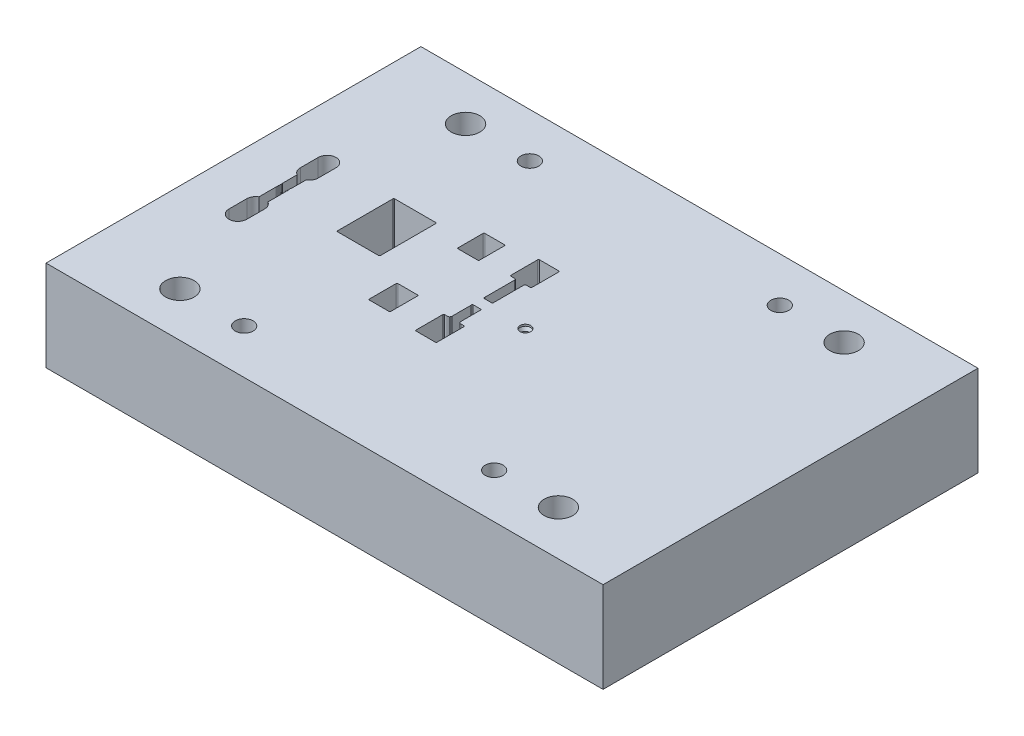
SolidWorks part; units mm, degrees
ref_plane "Front" through (0, 0, 0) normal (0, 0, 1) x (1, 0, 0)
ref_plane "Top" through (0, 0, 0) normal (0, 1, 0) x (1, 0, 0)
ref_plane "Right" through (0, 0, 0) normal (1, 0, 0) x (0, 0, -1)
sketch "Sketch1" plane through (0, 0, 0) normal (0, 0, 1) x (1, 0, 0)
  line L1 (-78, 0) -> (78, 0)
  line L2 (-78, 0) -> (-78, 25.4)
  line L3 (-78, 25.4) -> (78, 25.4)
  line L4 (78, 0) -> (78, 25.4)
  dimension "D1" = 78
  dimension "D2" = 25.4
  dimension "D3" = 78
extrude "Extrude1" add sketch "Sketch1" along normal mid plane 105
hole_wizard "M6 Tapped Hole1" positions "Sketch3" profile "Sketch2" tap size "M6" standard "ISO"
sketch "Sketch3" plane through (0, 25.4, 0) normal (0, 1, 0) x (-1, 0, 0)
  point P1 (35, -40)
  point P4 (-35, -40)
  point P13 (-35, 40)
  point P16 (35, 40)
sketch "Sketch2" plane through (-35, 25.4, -40) normal (1, 0, 0) x (0, 0, 1)
  line L0 (0, 0) -> (0, 16.5022)
  line L1 (0, 16.5022) -> (2.5, 15)
  line L2 (2.5, 15) -> (2.5, 0)
  line L5 (2.5, 0) -> (0, 0)
  line L10 (0, 16.5022) -> (-2.5, 15) construction
  line L11 (0, -6.35) -> (0, 107.95) construction
  dimension "Tap Drill Dia." = 5
  dimension "Tap Drill Depth" = 15
  dimension "Drill Angle" = 118
cosmetic thread "Hole Thread1" parameters "D1"=10, "D2"=6
cosmetic thread "Hole Thread2" parameters "D1"=10, "D2"=6
cosmetic thread "Hole Thread5" parameters "D1"=10, "D2"=6
cosmetic thread "Hole Thread6" parameters "D1"=10, "D2"=6
hole_wizard "Hole1" positions "Sketch5" profile "Sketch4" legacy end condition through all
sketch "Sketch5" plane through (0, 25.4, 0) normal (0, 1, 0) x (-1, 0, 0)
  point P1 (53, -40)
  point P6 (53, 40)
  point P9 (-53, 40)
  point P12 (-53, -40)
sketch "Sketch4" plane through (-53, 25.4, -40) normal (1, 0, 0) x (0, 0, 1)
  line L0 (0, 0) -> (0, 25.4)
  line L1 (0, 25.4) -> (4, 25.4)
  line L2 (4, 25.4) -> (4, 0)
  line L3 (4, 0) -> (0, 0)
  line L4 (0, 110) -> (0, -10) construction
  dimension "Diameter" = 8
  dimension "Depth" = 25.4
sketch "Sketch6" plane through (0, 25.4, 0) normal (0, 1, 0) x (1, 0, 0)
  line L0 (-61.75, -6.7884) -> (-61.5151, -7.4339)
  line L2 (-64.25, -6.7884) -> (-64.4849, -7.4339)
  line L4 (-18.25, -8.1954) -> (-23.75, -8.1954)
  line L5 (-24, -8.4454) -> (-24, -15.9454)
  line L6 (-23.75, -16.1954) -> (-18.25, -16.1954)
  line L7 (-18, -15.9454) -> (-18, -8.4454)
  line L8 (-18.25, -8.1954) -> (-23.75, -8.1954)
  line L9 (-24, -8.4454) -> (-24, -15.9454)
  line L10 (-23.75, -16.1954) -> (-18.25, -16.1954)
  line L11 (-18, -15.9454) -> (-18, -8.4454)
  line L12 (-18.25, 16.15) -> (-23.75, 16.15)
  line L13 (-24, 15.9) -> (-24, 8.9)
  line L14 (-23.75, 8.65) -> (-18.25, 8.65)
  line L15 (-18, 8.9) -> (-18, 15.9)
  line L16 (-18.25, 16.15) -> (-23.75, 16.15)
  line L17 (-24, 15.9) -> (-24, 8.9)
  line L18 (-23.75, 8.65) -> (-18.25, 8.65)
  line L19 (-18, 8.9) -> (-18, 15.9)
  line L20 (-33, -3.8454) -> (-33, 11.6546)
  line L21 (-39, -4.0954) -> (-33.25, -4.0954)
  line L22 (-39, 11.9046) -> (-39, -4.0954)
  line L23 (-33.25, 11.9046) -> (-39, 11.9046)
  line L24 (-33, -3.8454) -> (-33, 11.6546)
  line L28 (-44.75, -4.0954) -> (-39, -4.0954)
  line L29 (-39, -4.0954) -> (-39, 11.9046)
  line L30 (-39, 11.9046) -> (-44.75, 11.9046)
  line L31 (-45, 11.6546) -> (-45, -3.8454)
  line L32 (-44.75, -4.0954) -> (-33.25, -4.0954)
  line L34 (-33.25, 11.9046) -> (-44.75, 11.9046)
  line L35 (-45, 11.6546) -> (-45, -3.8454)
  line L38 (-61.75, -3.1454) -> (-61.75, -1.7954)
  line L39 (-61.75, 0.0046) -> (-61.75, 0.6066)
  line L40 (-62, 0.8566) -> (-64, 0.8566)
  line L41 (-64.25, 0.6066) -> (-64.25, 0.0046)
  line L42 (-64.25, -1.7954) -> (-64.25, -3.1454)
  line L43 (-64, -3.3954) -> (-62, -3.3954)
  line L44 (-9, -9.1754) -> (-9.7, -9.1754)
  line L45 (-9.95, -9.4254) -> (-9.95, -16.9254)
  line L46 (-9.7, -17.1754) -> (-4.3, -17.1754)
  line L47 (-4.05, -16.9254) -> (-4.05, -9.4254)
  line L48 (-4.3, -9.1754) -> (-5, -9.1754)
  line L49 (-5.6073, -8.9669) -> (-5.7285, -8.582)
  line L50 (-5.74, -8.5069) -> (-5.74, -3.2709)
  line L51 (-5.7249, -3.1854) -> (-5.7051, -3.1309)
  line L52 (-5.94, -2.7954) -> (-8.06, -2.7954)
  line L53 (-8.2949, -3.1309) -> (-8.2751, -3.1854)
  line L54 (-8.26, -3.2709) -> (-8.26, -8.5069)
  line L55 (-8.2715, -8.582) -> (-8.3927, -8.9669)
  line L56 (-9, -9.1754) -> (-9.7, -9.1754)
  line L57 (-9.95, -9.4254) -> (-9.95, -16.9254)
  line L58 (-9.7, -17.1754) -> (-4.3, -17.1754)
  line L59 (-4.05, -16.9254) -> (-4.05, -9.4254)
  line L60 (-4.3, -9.1754) -> (-5, -9.1754)
  line L61 (-5.6073, -8.9669) -> (-5.7285, -8.582)
  line L62 (-5.74, -8.5069) -> (-5.74, -3.2709)
  line L63 (-5.7249, -3.1854) -> (-5.7051, -3.1309)
  line L64 (-5.94, -2.7954) -> (-8.06, -2.7954)
  line L65 (-8.2949, -3.1309) -> (-8.2751, -3.1854)
  line L66 (-8.26, -3.2709) -> (-8.26, -8.5069)
  line L67 (-8.2715, -8.582) -> (-8.3927, -8.9669)
  line L68 (-5.4106, 9.4) -> (-4.3, 9.4)
  line L69 (-5.7003, 9.1618) -> (-5.6209, 9.2852)
  line L70 (-5.74, 0.7046) -> (-5.74, 9.0266)
  line L71 (-5.7151, 0.5921) -> (-5.7249, 0.6191)
  line L72 (-8.05, 0.2566) -> (-5.95, 0.2566)
  line L73 (-8.2751, 0.6191) -> (-8.2849, 0.5921)
  line L74 (-8.26, 9.0266) -> (-8.26, 0.7046)
  line L75 (-8.3791, 9.2852) -> (-8.2997, 9.1618)
  line L76 (-9.7, 9.4) -> (-8.5894, 9.4)
  line L77 (-9.95, 17.15) -> (-9.95, 9.65)
  line L78 (-4.3, 17.4) -> (-9.7, 17.4)
  line L79 (-4.05, 9.65) -> (-4.05, 17.15)
  line L80 (-5.4106, 9.4) -> (-4.3, 9.4)
  line L81 (-5.7003, 9.1618) -> (-5.6209, 9.2852)
  line L82 (-5.74, 0.7046) -> (-5.74, 9.0266)
  line L83 (-5.7151, 0.5921) -> (-5.7249, 0.6191)
  line L84 (-8.05, 0.2566) -> (-5.95, 0.2566)
  line L85 (-8.2751, 0.6191) -> (-8.2849, 0.5921)
  line L86 (-8.26, 9.0266) -> (-8.26, 0.7046)
  line L87 (-8.3791, 9.2852) -> (-8.2997, 9.1618)
  line L88 (-9.7, 9.4) -> (-8.5894, 9.4)
  line L89 (-9.95, 17.15) -> (-9.95, 9.65)
  line L90 (-4.3, 17.4) -> (-9.7, 17.4)
  line L91 (-4.05, 9.65) -> (-4.05, 17.15)
  line L92 (-61.75, -6.7884) -> (-61.75, -1.7954)
  line L93 (-61.75, 0.0046) -> (-61.75, 4.2497)
  line L95 (-64.25, 4.2497) -> (-64.25, 0.0046)
  line L96 (-64.25, -1.7954) -> (-64.25, -6.7884)
  line L162 (-61.75, -7.7694) -> (-64.25, -7.7694) construction
  line L163 (-64.25, 5.2306) -> (-61.75, 5.2306) construction
  line L164 (-61.75, -7.7694) -> (-64.25, -7.7694)
  line L165 (-64.25, 5.2306) -> (-61.75, 5.2306)
  line L166 (-64.25, 7.2306) -> (-64.25, 0.0046) construction
  line L167 (-64.25, 4.2497) -> (-64.4849, 4.8951)
  line L168 (-63, 5.2306) -> (-63, 5.7564) construction
  line L169 (-61.75, 4.2497) -> (-61.5151, 4.8951)
  line L170 (-63, 5.2306) -> (-63, -7.7694) construction
  line L171 (-63, -1.2694) -> (-59.6995, -1.2694) construction
  arc A0 (-61.5151, -7.4339) -> (-61.75, -7.7694) centre (-61.75, -7.5194) cw
  arc A1 (-64.4849, -7.4339) -> (-64.25, -7.7694) centre (-64.25, -7.5194) ccw
  arc A2 (-33.25, -4.0954) -> (-33, -3.8454) centre (-33.25, -3.8454) ccw
  arc A3 (-33, 11.6546) -> (-33.25, 11.9046) centre (-33.25, 11.6546) ccw
  arc A4 (-23.75, -8.1954) -> (-24, -8.4454) centre (-23.75, -8.4454) ccw
  arc A5 (-24, -15.9454) -> (-23.75, -16.1954) centre (-23.75, -15.9454) ccw
  arc A6 (-18.25, -16.1954) -> (-18, -15.9454) centre (-18.25, -15.9454) ccw
  arc A7 (-18, -8.4454) -> (-18.25, -8.1954) centre (-18.25, -8.4454) ccw
  arc A8 (-23.75, -8.1954) -> (-24, -8.4454) centre (-23.75, -8.4454) ccw
  arc A9 (-24, -15.9454) -> (-23.75, -16.1954) centre (-23.75, -15.9454) ccw
  arc A10 (-18.25, -16.1954) -> (-18, -15.9454) centre (-18.25, -15.9454) ccw
  arc A11 (-18, -8.4454) -> (-18.25, -8.1954) centre (-18.25, -8.4454) ccw
  arc A12 (-23.75, 16.15) -> (-24, 15.9) centre (-23.75, 15.9) ccw
  arc A13 (-24, 8.9) -> (-23.75, 8.65) centre (-23.75, 8.9) ccw
  arc A14 (-18.25, 8.65) -> (-18, 8.9) centre (-18.25, 8.9) ccw
  arc A15 (-18, 15.9) -> (-18.25, 16.15) centre (-18.25, 15.9) ccw
  arc A16 (-23.75, 16.15) -> (-24, 15.9) centre (-23.75, 15.9) ccw
  arc A17 (-24, 8.9) -> (-23.75, 8.65) centre (-23.75, 8.9) ccw
  arc A18 (-18.25, 8.65) -> (-18, 8.9) centre (-18.25, 8.9) ccw
  arc A19 (-18, 15.9) -> (-18.25, 16.15) centre (-18.25, 15.9) ccw
  arc A20 (-33.25, -4.0954) -> (-33, -3.8454) centre (-33.25, -3.8454) ccw
  arc A21 (-33, 11.6546) -> (-33.25, 11.9046) centre (-33.25, 11.6546) ccw
  arc A22 (-44.75, 11.9046) -> (-45, 11.6546) centre (-44.75, 11.6546) ccw
  arc A23 (-45, -3.8454) -> (-44.75, -4.0954) centre (-44.75, -3.8454) ccw
  arc A24 (-44.75, 11.9046) -> (-45, 11.6546) centre (-44.75, 11.6546) ccw
  arc A25 (-45, -3.8454) -> (-44.75, -4.0954) centre (-44.75, -3.8454) ccw
  arc A38 (-5.4106, 9.4) -> (-5.6209, 9.2852) centre (-5.4106, 9.15) ccw
  arc A39 (-5.7003, 9.1618) -> (-5.74, 9.0266) centre (-5.49, 9.0266) ccw
  arc A40 (-5.74, 0.7046) -> (-5.7249, 0.6191) centre (-5.49, 0.7046) ccw
  arc A41 (-5.95, 0.2566) -> (-5.7151, 0.5921) centre (-5.95, 0.5066) ccw
  arc A42 (-9.7, -9.1754) -> (-9.95, -9.4254) centre (-9.7, -9.4254) ccw
  arc A43 (-9.95, -16.9254) -> (-9.7, -17.1754) centre (-9.7, -16.9254) ccw
  arc A44 (-4.3, -17.1754) -> (-4.05, -16.9254) centre (-4.3, -16.9254) ccw
  arc A45 (-4.05, -9.4254) -> (-4.3, -9.1754) centre (-4.3, -9.4254) ccw
  arc A46 (-5.4806, -9.0963) -> (-5, -9.1754) centre (-5, -7.6754) ccw
  arc A47 (-5.5312, -9.0707) -> (-5.4806, -9.0963) centre (-5.4165, -8.9068) ccw
  arc A48 (-5.6073, -8.9669) -> (-5.5312, -9.0707) centre (-5.4165, -8.9068) ccw
  arc A49 (-5.74, -8.5069) -> (-5.7285, -8.582) centre (-5.49, -8.5069) ccw
  arc A50 (-5.7249, -3.1854) -> (-5.74, -3.2709) centre (-5.49, -3.2709) ccw
  arc A51 (-5.7051, -3.1309) -> (-5.94, -2.7954) centre (-5.94, -3.0454) ccw
  arc A52 (-8.06, -2.7954) -> (-8.2949, -3.1309) centre (-8.06, -3.0454) ccw
  arc A53 (-8.26, -3.2709) -> (-8.2751, -3.1854) centre (-8.51, -3.2709) ccw
  arc A54 (-8.2715, -8.582) -> (-8.26, -8.5069) centre (-8.51, -8.5069) ccw
  arc A55 (-8.4688, -9.0707) -> (-8.3927, -8.9669) centre (-8.5835, -8.9068) ccw
  arc A56 (-8.5194, -9.0963) -> (-8.4688, -9.0707) centre (-8.5835, -8.9068) ccw
  arc A57 (-9, -9.1754) -> (-8.5194, -9.0963) centre (-9, -7.6754) ccw
  arc A58 (-9.7, -9.1754) -> (-9.95, -9.4254) centre (-9.7, -9.4254) ccw
  arc A59 (-9.95, -16.9254) -> (-9.7, -17.1754) centre (-9.7, -16.9254) ccw
  arc A60 (-4.3, -17.1754) -> (-4.05, -16.9254) centre (-4.3, -16.9254) ccw
  arc A61 (-4.05, -9.4254) -> (-4.3, -9.1754) centre (-4.3, -9.4254) ccw
  arc A62 (-5.4806, -9.0963) -> (-5, -9.1754) centre (-5, -7.6754) ccw
  arc A63 (-5.5312, -9.0707) -> (-5.4806, -9.0963) centre (-5.4165, -8.9068) ccw
  arc A64 (-5.6073, -8.9669) -> (-5.5312, -9.0707) centre (-5.4165, -8.9068) ccw
  arc A65 (-5.74, -8.5069) -> (-5.7285, -8.582) centre (-5.49, -8.5069) ccw
  arc A66 (-5.7249, -3.1854) -> (-5.74, -3.2709) centre (-5.49, -3.2709) ccw
  arc A67 (-5.7051, -3.1309) -> (-5.94, -2.7954) centre (-5.94, -3.0454) ccw
  arc A68 (-8.06, -2.7954) -> (-8.2949, -3.1309) centre (-8.06, -3.0454) ccw
  arc A69 (-8.26, -3.2709) -> (-8.2751, -3.1854) centre (-8.51, -3.2709) ccw
  arc A70 (-8.2715, -8.582) -> (-8.26, -8.5069) centre (-8.51, -8.5069) ccw
  arc A71 (-8.4688, -9.0707) -> (-8.3927, -8.9669) centre (-8.5835, -8.9068) ccw
  arc A72 (-8.5194, -9.0963) -> (-8.4688, -9.0707) centre (-8.5835, -8.9068) ccw
  arc A73 (-9, -9.1754) -> (-8.5194, -9.0963) centre (-9, -7.6754) ccw
  arc A74 (-8.2849, 0.5921) -> (-8.05, 0.2566) centre (-8.05, 0.5066) ccw
  arc A75 (-8.2751, 0.6191) -> (-8.26, 0.7046) centre (-8.51, 0.7046) ccw
  arc A76 (-8.26, 9.0266) -> (-8.2997, 9.1618) centre (-8.51, 9.0266) ccw
  arc A77 (-8.3791, 9.2852) -> (-8.5894, 9.4) centre (-8.5894, 9.15) ccw
  arc A78 (-9.95, 9.65) -> (-9.7, 9.4) centre (-9.7, 9.65) ccw
  arc A79 (-9.7, 17.4) -> (-9.95, 17.15) centre (-9.7, 17.15) ccw
  arc A80 (-4.05, 17.15) -> (-4.3, 17.4) centre (-4.3, 17.15) ccw
  arc A81 (-4.3, 9.4) -> (-4.05, 9.65) centre (-4.3, 9.65) ccw
  arc A82 (-5.4106, 9.4) -> (-5.6209, 9.2852) centre (-5.4106, 9.15) ccw
  arc A83 (-5.7003, 9.1618) -> (-5.74, 9.0266) centre (-5.49, 9.0266) ccw
  arc A84 (-5.74, 0.7046) -> (-5.7249, 0.6191) centre (-5.49, 0.7046) ccw
  arc A85 (-5.95, 0.2566) -> (-5.7151, 0.5921) centre (-5.95, 0.5066) ccw
  arc A86 (-8.2849, 0.5921) -> (-8.05, 0.2566) centre (-8.05, 0.5066) ccw
  arc A87 (-8.2751, 0.6191) -> (-8.26, 0.7046) centre (-8.51, 0.7046) ccw
  arc A88 (-8.26, 9.0266) -> (-8.2997, 9.1618) centre (-8.51, 9.0266) ccw
  arc A89 (-8.3791, 9.2852) -> (-8.5894, 9.4) centre (-8.5894, 9.15) ccw
  arc A90 (-9.95, 9.65) -> (-9.7, 9.4) centre (-9.7, 9.65) ccw
  arc A91 (-9.7, 17.4) -> (-9.95, 17.15) centre (-9.7, 17.15) ccw
  arc A92 (-4.05, 17.15) -> (-4.3, 17.4) centre (-4.3, 17.15) ccw
  arc A93 (-4.3, 9.4) -> (-4.05, 9.65) centre (-4.3, 9.65) ccw
  arc A100 (-61.75, -1.7954) -> (-61.8, -1.6454) centre (-62, -1.7954) ccw
  arc A101 (-61.8, -1.3454) -> (-61.8, -1.6454) centre (-61.6, -1.4954) ccw
  arc A102 (-61.8, -1.3454) -> (-61.8, -1.0454) centre (-62, -1.1954) ccw
  arc A103 (-61.8, -0.7454) -> (-61.8, -1.0454) centre (-61.6, -0.8954) ccw
  arc A104 (-61.8, -0.7454) -> (-61.8, -0.4454) centre (-62, -0.5954) ccw
  arc A105 (-61.8, -0.1454) -> (-61.8, -0.4454) centre (-61.6, -0.2954) ccw
  arc A106 (-61.8, -0.1454) -> (-61.75, 0.0046) centre (-62, 0.0046) ccw
  arc A107 (-61.75, 0.6066) -> (-62, 0.8566) centre (-62, 0.6066) ccw
  arc A108 (-64, 0.8566) -> (-64.25, 0.6066) centre (-64, 0.6066) ccw
  arc A109 (-64.25, 0.0046) -> (-64.2, -0.1454) centre (-64, 0.0046) ccw
  arc A110 (-64.2, -0.4454) -> (-64.2, -0.1454) centre (-64.4, -0.2954) ccw
  arc A111 (-64.2, -0.4454) -> (-64.2, -0.7454) centre (-64, -0.5954) ccw
  arc A112 (-64.2, -1.0454) -> (-64.2, -0.7454) centre (-64.4, -0.8954) ccw
  arc A113 (-64.2, -1.0454) -> (-64.2, -1.3454) centre (-64, -1.1954) ccw
  arc A114 (-64.2, -1.6454) -> (-64.2, -1.3454) centre (-64.4, -1.4954) ccw
  arc A115 (-64.2, -1.6454) -> (-64.25, -1.7954) centre (-64, -1.7954) ccw
  arc A116 (-64.25, -3.1454) -> (-64, -3.3954) centre (-64, -3.1454) ccw
  arc A117 (-62, -3.3954) -> (-61.75, -3.1454) centre (-62, -3.1454) ccw
  arc A118 (-61.75, -1.7954) -> (-61.8, -1.6454) centre (-62, -1.7954) ccw
  arc A119 (-61.8, -1.3454) -> (-61.8, -1.6454) centre (-61.6, -1.4954) ccw
  arc A120 (-61.8, -1.3454) -> (-61.8, -1.0454) centre (-62, -1.1954) ccw
  arc A121 (-61.8, -0.7454) -> (-61.8, -1.0454) centre (-61.6, -0.8954) ccw
  arc A122 (-61.8, -0.7454) -> (-61.8, -0.4454) centre (-62, -0.5954) ccw
  arc A123 (-61.8, -0.1454) -> (-61.8, -0.4454) centre (-61.6, -0.2954) ccw
  arc A124 (-61.8, -0.1454) -> (-61.75, 0.0046) centre (-62, 0.0046) ccw
  arc A127 (-64.25, 0.0046) -> (-64.2, -0.1454) centre (-64, 0.0046) ccw
  arc A128 (-64.2, -0.4454) -> (-64.2, -0.1454) centre (-64.4, -0.2954) ccw
  arc A129 (-64.2, -0.4454) -> (-64.2, -0.7454) centre (-64, -0.5954) ccw
  arc A130 (-64.2, -1.0454) -> (-64.2, -0.7454) centre (-64.4, -0.8954) ccw
  arc A131 (-64.2, -1.0454) -> (-64.2, -1.3454) centre (-64, -1.1954) ccw
  arc A132 (-64.2, -1.6454) -> (-64.2, -1.3454) centre (-64.4, -1.4954) ccw
  arc A133 (-64.2, -1.6454) -> (-64.25, -1.7954) centre (-64, -1.7954) ccw
  arc A210 (-64.4849, 4.8951) -> (-64.25, 5.2306) centre (-64.25, 4.9806) cw
  arc A211 (-61.5151, 4.8951) -> (-61.75, 5.2306) centre (-61.75, 4.9806) ccw
  dimension "D5" = 0.25
  dimension "D9" = 20
  dimension "D1" = 0
  dimension "D2" = 0
  dimension "D3" = 0
  dimension "D4" = 0
  dimension "D6" = 0
  dimension "D7" = 0
  dimension "D8" = 0
extrude "Cut-Extrude1" cut sketch "Sketch6" against normal through all
sketch "Sketch7" plane through (0, 25.4, 0) normal (0, 1, 0) x (1, 0, 0)
  line L0 (-63, -7.7694) -> (-63, 6.2306) construction
  line L1 (-64.25, -7.7694) -> (-61.75, -7.7694) construction
  line L2 (-63, 5.2306) -> (-63, -8.7694) construction
  line L4 (-63, 6.2306) -> (-63, 11.2306) construction
  line L5 (-65.5, 6.2306) -> (-65.5, 11.2306)
  line L6 (-60.5, 6.2306) -> (-60.5, 11.2306)
  line L7 (-63, -8.7694) -> (-63, -13.7694) construction
  line L8 (-60.5, -8.7694) -> (-60.5, -13.7694)
  line L9 (-65.5, -8.7694) -> (-65.5, -13.7694)
  line L10 (-62.5414, 5.2306) -> (-62.5414, -7.7694) construction
  line L11 (-61.75, 5.2306) -> (-64.25, 5.2306) construction
  line L12 (-64.25, -7.7694) -> (-61.75, -7.7694) construction
  line L13 (-62.5414, -1.2694) -> (-59.6733, -1.2694) construction
  line L14 (-63, 8.7306) -> (-59.6733, 8.7306) construction
  line L15 (-63, -11.2694) -> (-59.6733, -11.2694) construction
  line L16 (-59.6733, -11.2694) -> (-59.6733, 8.7306) construction
  arc A0 (-65.5, 6.2306) -> (-60.5, 6.2306) centre (-63, 6.2306) ccw
  arc A1 (-60.5, 11.2306) -> (-65.5, 11.2306) centre (-63, 11.2306) ccw
  arc A2 (-60.5, -8.7694) -> (-65.5, -8.7694) centre (-63, -8.7694) ccw
  arc A3 (-65.5, -13.7694) -> (-60.5, -13.7694) centre (-63, -13.7694) ccw
  point P1 (-63, 8.7306)
  point P14 (-63, -11.2694)
  dimension "D1" = 5
  dimension "D2" = 15
  dimension "D3" = 5
  dimension "D4" = 5
  dimension "D5" = 5
extrude "Cut-Extrude2" cut sketch "Sketch7" against normal blind 8
fillet "Fillet2" radius 0.25 10 edges at (-61.6325, 17.4, 7.1112) (-61.5452, 17.4, 7.6628) (-64.3675, 17.4, 7.1112) (-64.4548, 17.4, 7.6628) (-64.3675, 17.4, -4.5724) (-64.4548, 17.4, -5.124) (-61.6325, 17.4, -4.5724) (-61.5452, 17.4, -5.124) (-63, 17.4, 7.7694) (-63, 17.4, -5.2306)
hole_wizard "Hole2" positions "Sketch9" profile "Sketch8" legacy
sketch "Sketch9" plane through (0, 25.4, 0) normal (0, 1, 0) x (1, 0, 0)
  point P0 (5, -1.2694)
sketch "Sketch8" plane through (5, 25.4, 1.2694) normal (1, 0, 0) x (0, 0, 1)
  line L0 (0, 0) -> (0, 100)
  line L1 (0, 100) -> (1, 100)
  line L2 (1, 100) -> (1, 1.366)
  line L3 (1, 1.366) -> (1.5, 0.5)
  line L4 (1.5, 0.5) -> (1.5, 0)
  line L5 (1.5, 0) -> (0, 0)
  line L6 (0, -6.13) -> (0, 109.2824) construction
  line L7 (-1, 1.366) -> (-1.5, 0.5) construction
  line L8 (0, 100) -> (-1, 100) construction
  dimension "Diameter" = 2
  dimension "Depth" = 100
  dimension "C-Drill Diameter" = 3
  dimension "C-Drill Depth" = 0.5
  dimension "C-Drill Angle" = 60
hole_wizard "Hole3" positions "Sketch11" profile "Sketch10" legacy
sketch "Sketch11" plane through (0, 0, 0) normal (0, -1, 0) x (-1, 0, 0)
  point P0 (42, -16)
sketch "Sketch10" plane through (-42, 0, 16) normal (1, 0, 0) x (0, 0, -1)
  line L0 (0, 0) -> (0, 5)
  line L1 (0, 5) -> (5, 5)
  line L2 (5, 5) -> (5, 0)
  line L3 (5, 0) -> (0, 0)
  line L4 (0, 110) -> (0, -10) construction
  dimension "Diameter" = 10
  dimension "Depth" = 5
